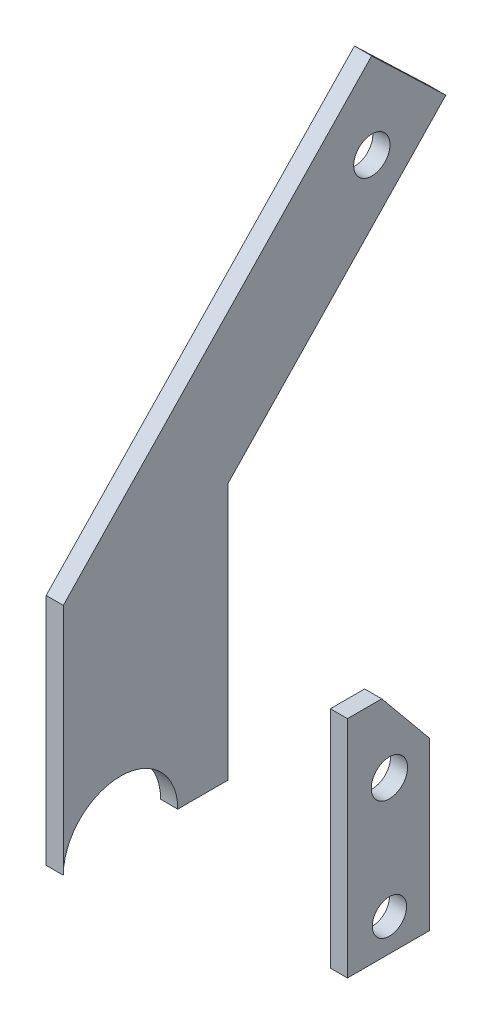
SolidWorks part; units mm, degrees
ref_plane "Alzado" through (0, 0, 0) normal (0, 0, 1) x (1, 0, 0)
ref_plane "Planta" through (0, 0, 0) normal (0, 1, 0) x (1, 0, 0)
ref_plane "Vista lateral" through (0, 0, 0) normal (1, 0, 0) x (0, 0, -1)
sketch "Croquis1" plane through (0, 0, 0) normal (1, 0, 0) x (0, 0, -1)
  line L0 (63.5132, 141.3043) -> (35.8346, 112.4271)
  line L1 (63.5132, 141.3043) -> (41.8552, 162.0633)
  line L2 (41.8552, 162.0633) -> (14.1766, 133.186)
  line L3 (-0.0217, 0.018) -> (-14.6992, 0.018)
  line L4 (35.8346, 112.4271) -> (-0.0217, 75.018)
  line L5 (-48.1002, 68.2122) -> (-48.1002, 0.018)
  line L6 (14.1766, 133.186) -> (-48.1002, 68.2122)
  line L7 (-0.0217, 75.018) -> (-0.0217, 0.018)
  line L8 (58.8026, -67.3956) -> (58.8026, -18.8378)
  line L9 (58.8026, -18.8378) -> (44.8119, -1.8596)
  line L10 (44.8119, -1.8596) -> (34.8119, -1.8596)
  line L11 (34.8119, -1.8596) -> (34.8119, -67.3956)
  line L12 (34.8119, -67.3956) -> (58.8026, -67.3956)
  circle A0 centre (41.9172, 136.9853) radius 5.3
  circle A1 centre (47.0454, -22.9327) radius 5.3
  arc A2 (-14.6992, 0.018) -> (-48.1002, 0.018) centre (-31.3997, 0.018) ccw
  circle A3 centre (47.0454, -57.9448) radius 5
  point P21 (0, 0)
  point P22 (0, 0)
extrude "Saliente-Extruir1" add sketch "Croquis1" along normal blind 5
